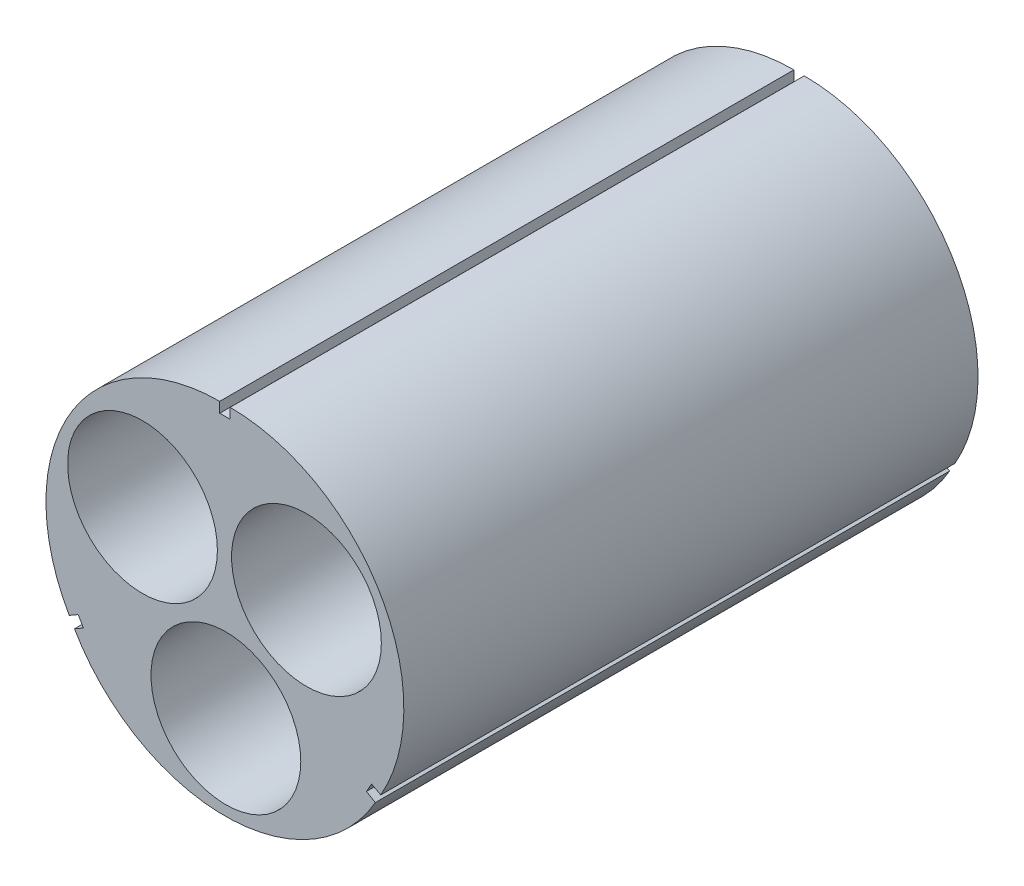
SolidWorks part; units mm, degrees
ref_plane "Front Plane" through (0, 0, 0) normal (0, 0, 1) x (1, 0, 0)
ref_plane "Top Plane" through (0, 0, 0) normal (0, 1, 0) x (1, 0, 0)
ref_plane "Right Plane" through (0, 0, 0) normal (1, 0, 0) x (0, 0, -1)
sketch "Sketch1" plane through (0, 0, 0) normal (0, 0, 1) x (1, 0, 0)
  line L0 (0, 0) -> (-20.1218, 11.3741) construction
  line L1 (0, 0) -> (19.9112, 11.7389) construction
  line L2 (0, 0) -> (0.2377, -23.114) construction
  line L3 (0, 0) -> (0, 25.4) construction
  line L4 (0, 0) -> (21.997, -12.7) construction
  line L5 (0, 0) -> (-21.997, -12.7) construction
  line L6 (0, 20.32) -> (-0.635, 20.32)
  line L7 (0, 20.32) -> (0.635, 20.32)
  line L8 (0.635, 20.32) -> (0.635, 21.5807)
  line L9 (-0.635, 20.32) -> (-0.635, 21.5807)
  line L10 (-17.5976, -10.16) -> (-17.2801, -10.7099)
  line L11 (-17.5976, -10.16) -> (-17.9151, -9.6101)
  line L12 (-17.2801, -10.7099) -> (-18.3719, -11.3403)
  line L13 (-17.9151, -9.6101) -> (-19.0069, -10.2404)
  line L14 (17.5976, -10.16) -> (17.2801, -10.7099)
  line L15 (17.5976, -10.16) -> (17.9151, -9.6101)
  line L16 (17.2801, -10.7099) -> (18.3719, -11.3403)
  line L17 (17.9151, -9.6101) -> (19.0255, -10.2057)
  circle A4 centre (0.1189, -11.557) radius 9.144
  circle A5 centre (9.9556, 5.8695) radius 9.144
  circle A6 centre (-10.0609, 5.687) radius 9.144
  arc A9 (-0.635, 21.5807) -> (-19.0069, -10.2404) centre (-0.635, 0.3666) ccw
  arc A10 (0.635, 21.5807) -> (19.0255, -10.2057) centre (0.635, 0.3674) cw
  arc A11 (18.3719, -11.3403) -> (-18.3719, -11.3403) centre (0, -0.7332) cw
  point P1 (2.188, 1.29)
  point P2 (-2.2112, 1.2499)
  point P6 (0.0261, -2.54)
  point P7 (9.9556, 5.8695)
  point P8 (-10.0609, 5.687)
  point P9 (0.1189, -11.557)
  point P18 (17.5976, -10.16)
  point P22 (-17.5976, -10.16)
  point P23 (0, 20.32)
  dimension "D1" = 2.54
  dimension "D2" = 20.32
  dimension "D3" = 2.54
  dimension "D4" = 9.017
  dimension "D5" = 9.017
  dimension "D7" = 120
  dimension "D6" = 9.017
  dimension "D8" = 120
  dimension "D9" = 20.32
  dimension "D10" = 20.32
  dimension "D11" = 90
  dimension "D12" = 90
  dimension "D13" = 90
  dimension "D14" = 90
extrude "Boss-Extrude1" add sketch "Sketch1" along normal blind 70.104
